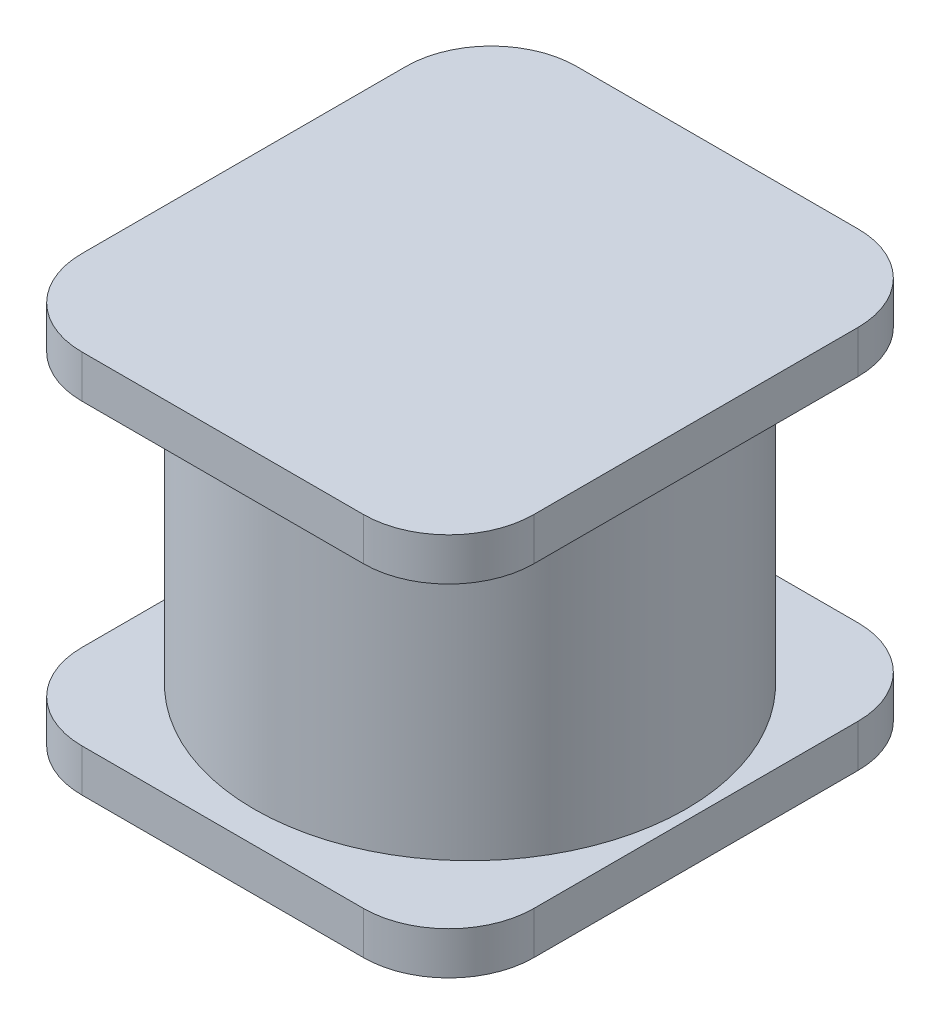
SolidWorks part; units mm, degrees
ref_plane "Front Plane" through (0, 0, 0) normal (0, 0, 1) x (1, 0, 0)
ref_plane "Top Plane" through (0, 0, 0) normal (0, 1, 0) x (1, 0, 0)
ref_plane "Right Plane" through (0, 0, 0) normal (1, 0, 0) x (0, 0, -1)
sketch "Sketch1" plane through (0, 0, 0) normal (0, 1, 0) x (1, 0, 0)
  line L1 (-2.65, -2.9) -> (2.65, -2.9)
  line L2 (-2.65, -2.9) -> (-2.65, 2.9)
  line L3 (-2.65, 2.9) -> (2.65, 2.9)
  line L4 (2.65, -2.9) -> (2.65, 2.9)
  line L5 (-2.65, -2.9) -> (2.65, 2.9) construction
  line L6 (-2.65, 2.9) -> (2.65, -2.9) construction
  point P0 (0, 0)
extrude "Boss-Extrude1" add sketch "Sketch1" along normal blind 0.5
sketch "Sketch2" plane through (0, 0.5, 0) normal (0, 1, 0) x (-1, 0, 0)
  circle A0 centre (0, 0) radius 2.5334
extrude "Boss-Extrude2" add sketch "Sketch2" along normal blind 3.5
sketch "Sketch3" plane through (0, 4, 0) normal (0, 1, 0) x (-1, 0, 0)
  line L1 (2.65, -2.9) -> (-2.65, -2.9)
  line L2 (2.65, -2.9) -> (2.65, 2.9)
  line L3 (2.65, 2.9) -> (-2.65, 2.9)
  line L4 (-2.65, -2.9) -> (-2.65, 2.9)
extrude "Boss-Extrude3" add sketch "Sketch3" along normal blind 0.5
fillet "Fillet1" radius 1 8 edges at (-2.65, 4.25, -2.9) (2.65, 4.25, -2.9) (2.65, 4.25, 2.9) (-2.65, 4.25, 2.9) (2.65, 0.25, -2.9) (2.65, 0.25, 2.9) (-2.65, 0.25, 2.9) (-2.65, 0.25, -2.9)
